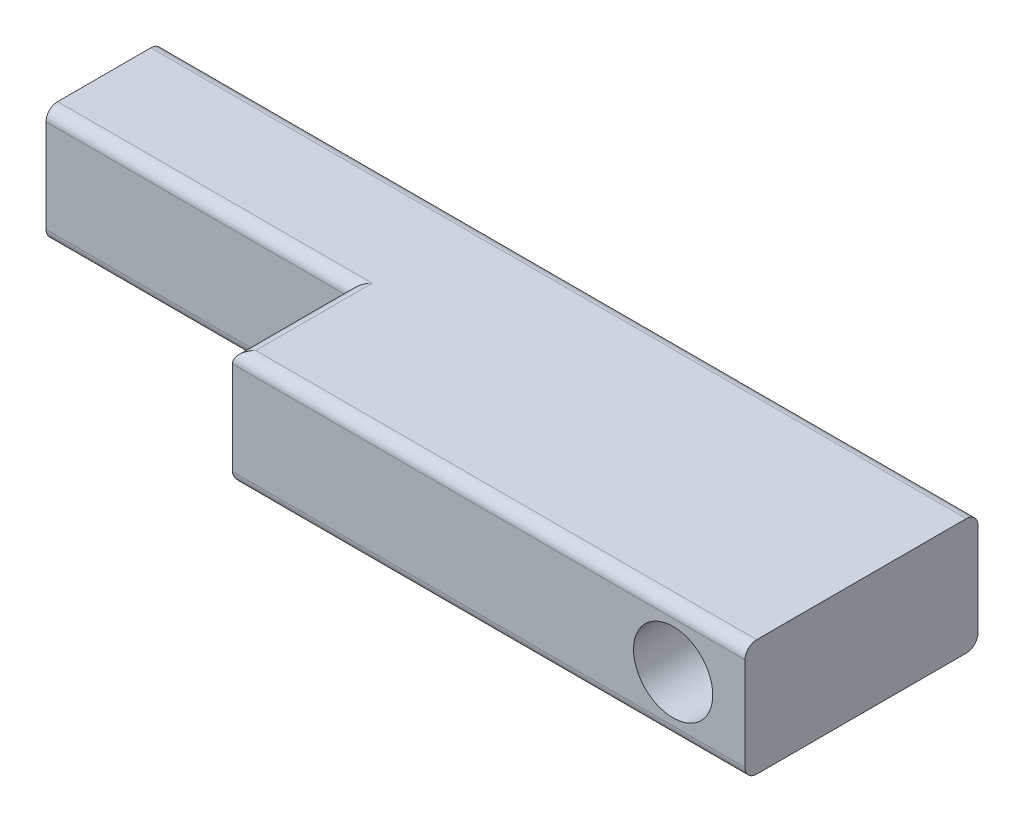
SolidWorks part; units mm, degrees
material "PLA"
ref_plane "Front Plane" through (0, 0, 0) normal (0, 0, 1) x (1, 0, 0)
ref_plane "Top Plane" through (0, 0, 0) normal (0, 1, 0) x (1, 0, 0)
ref_plane "Right Plane" through (0, 0, 0) normal (1, 0, 0) x (0, 0, -1)
sketch "Sketch1" plane through (0, 0, 0) normal (0, 0, 1) x (1, 0, 0)
  line L1 (-17.5, -2.5) -> (17.5, -2.5)
  line L2 (-17.5, -2.5) -> (-17.5, 2.5)
  line L3 (-17.5, 2.5) -> (17.5, 2.5)
  line L4 (17.5, -2.5) -> (17.5, 2.5)
  line L5 (-17.5, -2.5) -> (17.5, 2.5) construction
  line L6 (-17.5, 2.5) -> (17.5, -2.5) construction
  point P0 (0, 0)
  dimension "D1" = 35
  dimension "D2" = 5
extrude "Boss-Extrude1" add sketch "Sketch1" along normal blind 5
sketch "Sketch3" plane through (0, 0, 5) normal (0, 0, 1) x (1, 0, 0)
  line L0 (-17.5, -2.5) -> (17.5, -2.5) construction
  line L1 (17.5, 2.5) -> (-4.5, 2.5)
  line L2 (17.5, 2.5) -> (17.5, -2.5)
  line L3 (17.5, -2.5) -> (-4.5, -2.5)
  line L4 (-4.5, 2.5) -> (-4.5, -2.5)
  dimension "D1" = 22
extrude "Boss-Extrude3" add sketch "Sketch3" along normal blind 5
fillet "Fillet1" radius 0.5 8 edges at (-11, -2.5, 5) (-11, 2.5, 5) (6.5, -2.5, 10) (6.5, 2.5, 10) (0, -2.5, 0) (0, 2.5, 0) (-4.5, 2.5, 7.5) (-4.5, -2.5, 7.5)
sketch "Sketch5" plane through (0, 0, 0) normal (0, 0, -1) x (-1, 0, 0)
  circle A0 centre (-14.4153, 0) radius 1.5
  dimension "D1" = 3
hole_wizard "M3 Clearance Hole1" positions "3DSketch1" profile "Sketch6" hole size "M3" standard "ANSI Metric" end condition through all
sketch3d "3DSketch1"
  point P0 (14.4153, 0, 0)
sketch "Sketch6" plane through (14.4153, 0, 0) normal (1, 0, 0) x (0, 1, 0)
  line L0 (0, 0) -> (0, 10)
  line L1 (0, 10) -> (1.7, 10)
  line L2 (1.7, 10) -> (1.7, 0)
  line L5 (1.7, 0) -> (0, 0)
  line L11 (0, -6.35) -> (0, 107.95) construction
  dimension "Thru Hole Dia." = 3.4
  dimension "Thru Hole Depth" = 10
